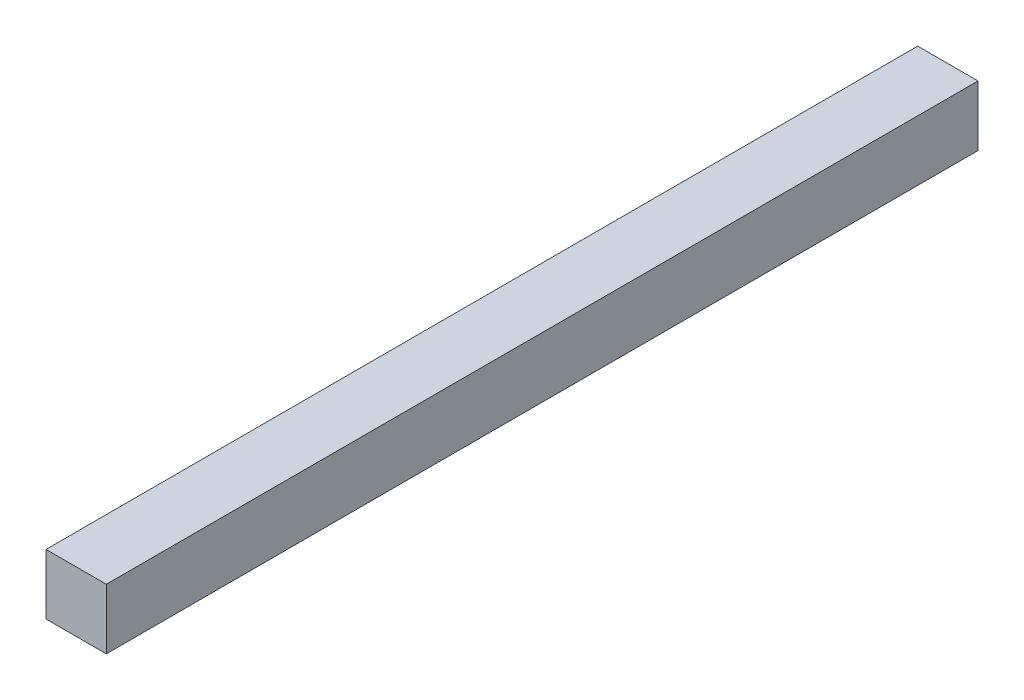
SolidWorks part; units mm, degrees
ref_plane "Ebene vorne" through (0, 0, 0) normal (0, 0, 1) x (1, 0, 0)
ref_plane "Ebene oben" through (0, 0, 0) normal (0, 1, 0) x (1, 0, 0)
ref_plane "Ebene rechts" through (0, 0, 0) normal (1, 0, 0) x (0, 0, -1)
sketch "Skizze1" plane through (0, 0, 0) normal (0, 0, 1) x (1, 0, 0)
  line L1 (-16.5, 16.5) -> (16.5, 16.5)
  line L2 (-16.5, 16.5) -> (-16.5, -16.5)
  line L3 (-16.5, -16.5) -> (16.5, -16.5)
  line L4 (16.5, 16.5) -> (16.5, -16.5)
  line L5 (-16.5, 16.5) -> (16.5, -16.5) construction
  line L6 (-16.5, -16.5) -> (16.5, 16.5) construction
  point P0 (0, 0)
  dimension "D1" = 33
  dimension "D2" = 33
extrude "Aufsatz-Linear austragen1" add sketch "Skizze1" along normal blind 477
hole_wizard "Ø7.0 (7) Durchmesser Bohrung1" positions "Skizze5" profile "Skizze6" hole size "Ø7.0" standard "ANSI Metrisch"
sketch "Skizze5" plane through (0, -16.5, 0) normal (0, -1, 0) x (-1, 0, 0)
  line L0 (16.5, -477) -> (16.5, 0) construction
  line L2 (16.5, -477) -> (-16.5, -477) construction
  line L3 (65.7482, -222) -> (-52.4464, -222) construction
  point P0 (0, -437)
  point P3 (0, -349.5)
  point P14 (0, -262)
  dimension "D1" = 16.5
  dimension "D2" = 40
  dimension "D3" = 0
  dimension "D4" = 40
  dimension "D5" = 87.5
  dimension "D6" = 255
sketch "Skizze6" plane through (0, -16.5, 437) normal (1, 0, 0) x (0, 0, -1)
  line L0 (0, 0) -> (0, 24.353)
  line L1 (0, 24.353) -> (3.5, 22.25)
  line L2 (3.5, 22.25) -> (3.5, 0)
  line L5 (3.5, 0) -> (0, 0)
  line L10 (0, 24.353) -> (-3.5, 22.25) construction
  line L11 (0, -6.35) -> (0, 107.95) construction
  dimension "Bohrerdurchmesser" = 7
  dimension "Bohrungstiefe" = 22.25
  dimension "Spitzenwinkel" = 118
